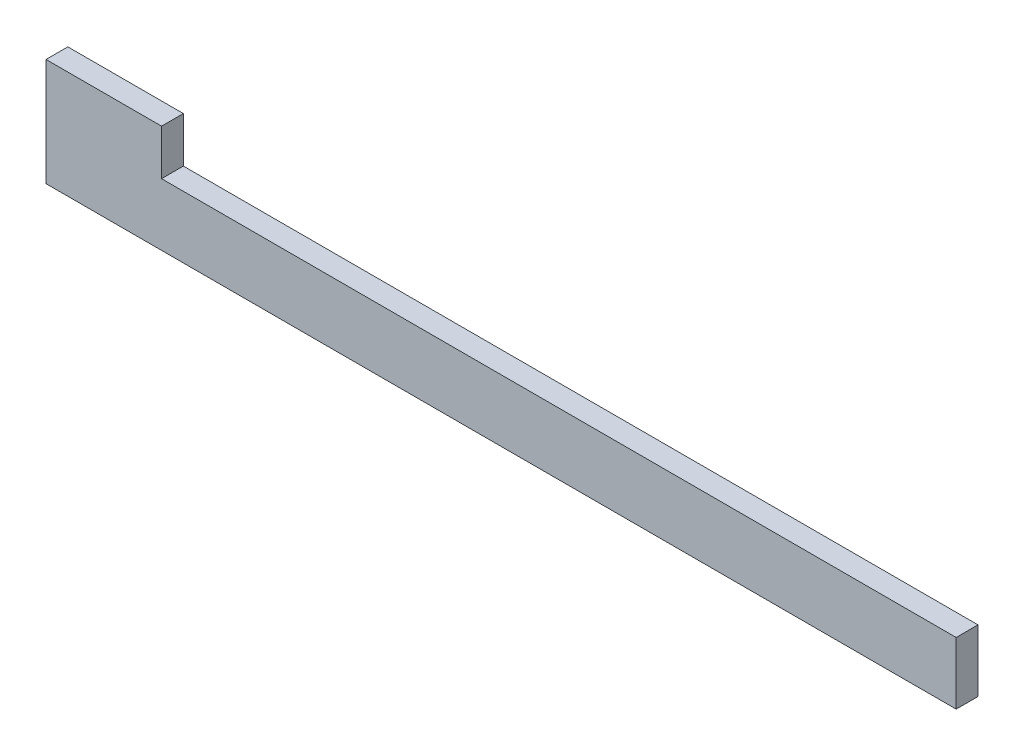
SolidWorks part; units mm, degrees
ref_plane "前视基准面" through (0, 0, 0) normal (0, 0, 1) x (1, 0, 0)
ref_plane "上视基准面" through (0, 0, 0) normal (0, 1, 0) x (1, 0, 0)
ref_plane "右视基准面" through (0, 0, 0) normal (1, 0, 0) x (0, 0, -1)
sketch "草图1" plane through (0, 0, 0) normal (0, 0, 1) x (1, 0, 0)
  line L0 (-82.5313, -18.4405) -> (-82.5313, 10)
  line L1 (-29.6146, 10) -> (334.3081, 10)
  line L2 (334.3081, 10) -> (334.3081, -18.4405)
  line L3 (334.3081, -18.4405) -> (-82.5313, -18.4405)
  line L4 (-82.5313, 10) -> (-82.5313, 30.8351)
  line L5 (-82.5313, 30.8351) -> (-29.6146, 30.8351)
  line L6 (-29.6146, 30.8351) -> (-29.6146, 10)
  line L7 (-56.0729, 30.8351) -> (-56.0729, 10) construction
extrude "凸台-拉伸1" add sketch "草图1" along normal blind 10
